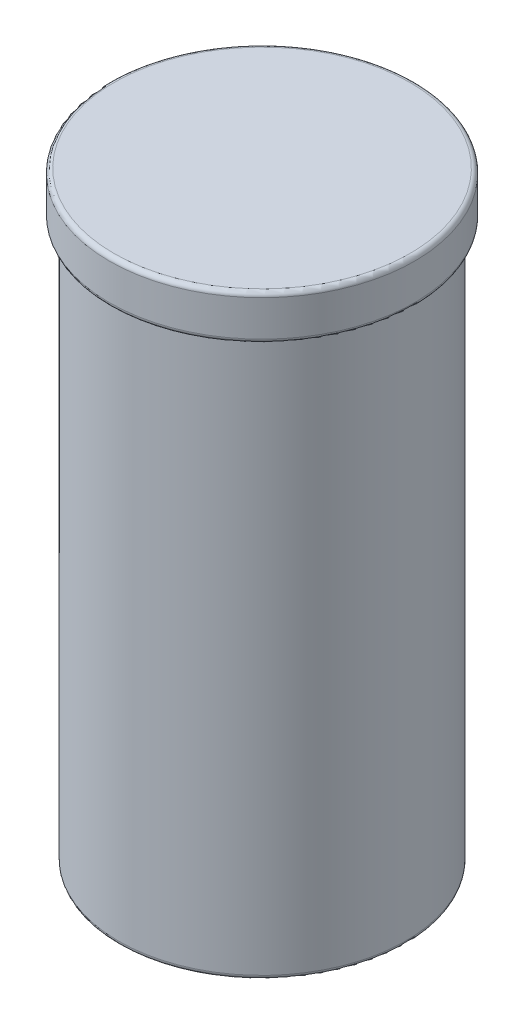
SolidWorks part; units mm, degrees
ref_plane "Front Plane" through (0, 0, 0) normal (0, 0, 1) x (1, 0, 0)
ref_plane "Top Plane" through (0, 0, 0) normal (0, 1, 0) x (1, 0, 0)
ref_plane "Right Plane" through (0, 0, 0) normal (1, 0, 0) x (0, 0, -1)
sketch "Sketch1" plane through (0, 0, 0) normal (0, 1, 0) x (1, 0, 0)
  circle A0 centre (0, 0) radius 16
  dimension "D1" = 32
extrude "Boss-Extrude1" add sketch "Sketch1" along normal blind 67.12
sketch "Sketch2" plane through (0, 0, 0) normal (0, -1, 0) x (1, 0, 0)
  circle A1 centre (0, 0) radius 17
  circle A2 centre (0, 0) radius 16 construction
  circle A3 centre (0, 0) radius 16
  circle M1 centre (0, 0) radius 16
  dimension "D1" = 1
extrude "Boss-Extrude2" add sketch "Sketch2" along normal blind 5 from surface at -67.12 contours A1 M1 starting at face at (0, 67.12, 16)
fillet "Fillet1" radius 0.5 3 edges at (0, 0, 16) (0, 62.12, 17) (0, 67.12, 17)
